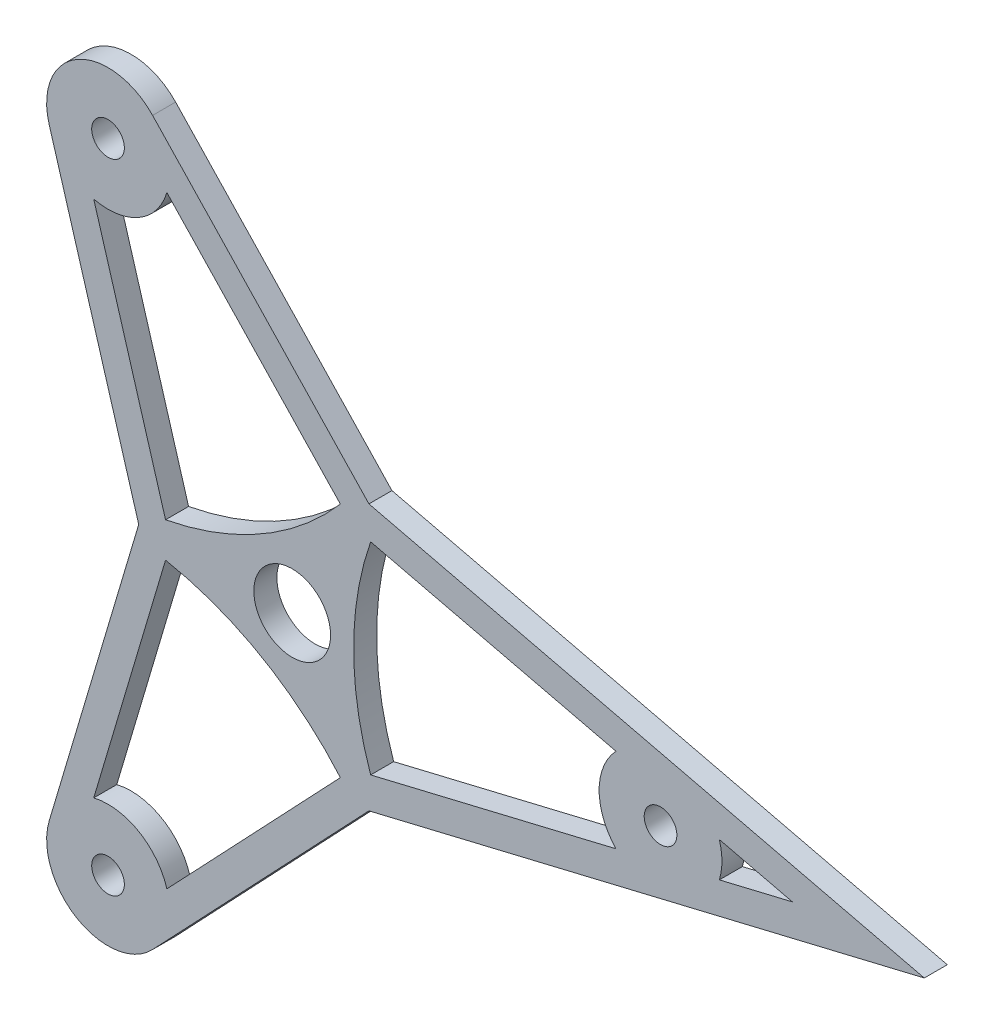
SolidWorks part; units mm, degrees
material "PVC 0.007 Plasticized"
ref_plane "Front Plane" through (0, 0, 0) normal (0, 0, 1) x (1, 0, 0)
ref_plane "Top Plane" through (0, 0, 0) normal (0, 1, 0) x (1, 0, 0)
ref_plane "Right Plane" through (0, 0, 0) normal (1, 0, 0) x (0, 0, -1)
sketch "Sketch1" plane through (0, 0, 0) normal (0, 0, 1) x (1, 0, 0)
  line L0 (93.017, 0) -> (-97.9083, 0) construction
  line L1 (0, 0) -> (-38.1, 65.9911) construction
  line L2 (0, 0) -> (-38.1, -65.9911) construction
  line L3 (0, 0) -> (38.1, 65.9911) construction
  line L4 (0, 0) -> (38.1, -65.9911) construction
  line L5 (-31.75, 0) -> (-50.2745, 62.3755)
  line L6 (-31.75, 0) -> (-50.2745, -62.3755)
  line L7 (15.875, -27.4963) -> (-28.8816, -74.7267)
  line L8 (15.875, -27.4963) -> (79.156, -12.3512)
  line L9 (15.875, 27.4963) -> (78.9112, 12.4098)
  line L10 (15.875, 27.4963) -> (-28.8816, 74.7267)
  line L11 (78.9112, 12.4098) -> (130.7632, 0)
  line L12 (79.156, -12.3512) -> (130.7632, 0)
  line L13 (9.9682, 24.4978) -> (-25.9255, 62.3755)
  line L14 (16.2316, 20.8816) -> (66.9816, 8.7356)
  line L15 (88.3745, 3.6156) -> (103.4816, 0)
  line L16 (88.3745, -3.6156) -> (103.4816, 0)
  line L17 (16.2316, -20.8816) -> (66.9816, -8.7356)
  line L18 (9.9682, -24.4978) -> (-25.9255, -62.3755)
  line L19 (-26.1998, -3.6162) -> (-41.056, -53.6399)
  line L20 (-26.1998, 3.6162) -> (-41.056, 53.6399)
  line L21 (-25.1259, 0) -> (-44.1872, -64.1833) construction
  line L22 (12.5629, -21.7597) -> (-33.4908, -70.3589) construction
  line L23 (77.678, -6.1756) -> (103.4816, 0) construction
  line L24 (77.4332, 6.2342) -> (103.4816, 0) construction
  line L25 (12.5629, 21.7597) -> (77.4332, 6.2342) construction
  line L27 (12.5629, -21.7597) -> (77.678, -6.1756) construction
  line L28 (12.5629, 21.7597) -> (-33.4908, 70.3589) construction
  line L29 (-25.1259, 0) -> (-44.1872, 64.1833) construction
  circle A0 centre (0, 0) radius 7.9375
  circle A1 centre (0, 0) radius 31.75 construction
  circle A2 centre (0, 0) radius 12.7 construction
  circle A3 centre (0, 0) radius 76.2 construction
  arc A4 (66.9816, 8.7356) -> (66.9816, -8.7356) centre (76.2, 0) ccw
  arc A6 (-50.2745, -62.3755) -> (-28.8816, -74.7267) centre (-38.1, -65.9911) ccw
  arc A7 (-28.8816, 74.7267) -> (-50.2745, 62.3755) centre (-38.1, 65.9911) ccw
  arc A8 (-25.9255, -62.3755) -> (-41.056, -53.6399) centre (-38.1, -65.9911) ccw
  arc A9 (88.3745, -3.6156) -> (88.3745, 3.6156) centre (76.2, 0) ccw
  arc A10 (-41.056, 53.6399) -> (-25.9255, 62.3755) centre (-38.1, 65.9911) ccw
  arc A12 (-32.5617, -2.7331) -> (13.9139, -29.5658) centre (-38.1, -65.9911) ccw construction
  arc A14 (13.9139, 29.5658) -> (-32.5617, 2.7331) centre (-38.1, 65.9911) ccw construction
  arc A19 (16.2316, 20.8816) -> (16.2316, -20.8816) centre (76.2, 0) ccw
  arc A20 (-26.1998, 3.6162) -> (9.9682, 24.4978) centre (-38.1, 65.9911) ccw
  arc A21 (18.6478, -26.8327) -> (18.6478, 26.8327) centre (76.2, 0) ccw construction
  arc A22 (9.9682, -24.4978) -> (-26.1998, -3.6162) centre (-38.1, -65.9911) ccw
  point P16 (0, 0)
  dimension "D1" = 15.875
  dimension "D2" = 63.5
  dimension "D3" = 25.4
  dimension "D4" = 152.4
  dimension "D5" = 25.4
  dimension "D6" = 3
  dimension "D7" = 60
  dimension "D8" = 60
  dimension "D9" = 6.35
  dimension "D10" = 6.35
extrude "Boss-Extrude1" add sketch "Sketch1" against normal blind 4.7625
hole_wizard "H (0.266) Diameter Hole1" positions "Sketch2" profile "Sketch3" hole size "H" standard "ANSI Inch" end condition through all
sketch "Sketch2" plane through (0, 0, 0) normal (0, 0, 1) x (1, 0, 0)
  point P0 (76.2, 0)
  point P3 (-38.1, 65.9911)
  point P6 (-38.1, -65.9911)
sketch "Sketch3" plane through (76.2, 0, 0) normal (1, 0, 0) x (0, -1, 0)
  line L0 (0, 0) -> (0, 4.7625)
  line L1 (0, 4.7625) -> (3.3782, 4.7625)
  line L2 (3.3782, 4.7625) -> (3.3782, 0)
  line L5 (3.3782, 0) -> (0, 0)
  line L11 (0, -6.35) -> (0, 107.95) construction
  dimension "Thru Hole Dia." = 6.7564
  dimension "Thru Hole Depth" = 4.7625
